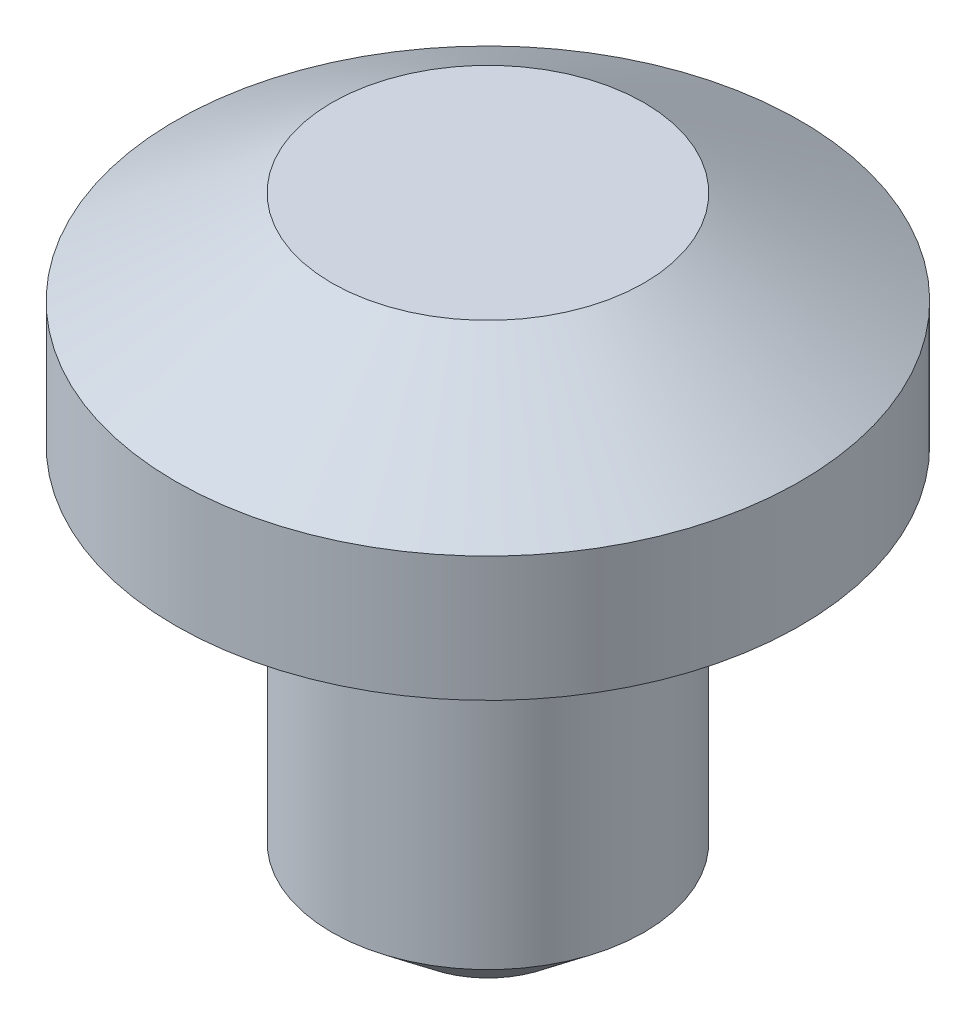
SolidWorks part; units mm, degrees
ref_plane "Front Plane" through (0, 0, 0) normal (0, 0, 1) x (1, 0, 0)
ref_plane "Top Plane" through (0, 0, 0) normal (0, 1, 0) x (1, 0, 0)
ref_plane "Right Plane" through (0, 0, 0) normal (1, 0, 0) x (0, 0, -1)
sketch "Sketch1" plane through (0, 0, 0) normal (0, 0, 1) x (1, 0, 0)
  line L0 (0, 63.5) -> (0, -63.5)
  line L1 (-31.75, -63.5) -> (0, -63.5)
  line L2 (-63.5, 0) -> (-63.5, 63.5)
  line L3 (-63.5, 63.5) -> (0, 63.5)
  line L4 (-63.5, 0) -> (-31.75, 0)
  line L5 (-31.75, 0) -> (-31.75, -63.5)
  line L6 (-63.5, 0) -> (0, 0) construction
  dimension "D2" = 63.5
  dimension "D4" = 31.75
  dimension "D3" = 63.5
revolve "Revolve1" add sketch "Sketch1" angle 360 about L0
sketch "Sketch3" plane through (0, 0, 0) normal (1, 0, 0) x (0, 0, -1)
  line L0 (-63.5, 0) -> (63.5, 0) construction
  line L1 (63.5, 63.5) -> (-63.5, 63.5) construction
  line L2 (-31.75, -63.5) -> (31.75, -63.5) construction
  line L3 (-63.5, 0) -> (63.5, 0)
  line L4 (0, 63.5) -> (-63.5, 63.5)
  line L5 (-31.75, -63.5) -> (0, -63.5)
  line L6 (-63.5, 63.5) -> (-63.5, 0)
  line L7 (-31.75, -63.5) -> (-31.75, 0)
  line L8 (-63.5, 19.05) -> (-90.7013, 19.05)
  line L9 (0, 63.5) -> (0, -63.5)
  line L10 (-63.5, 19.05) -> (-31.75, 0)
  line L11 (-90.7013, 44.45) -> (-63.5, 44.45)
  line L12 (-31.75, 0) -> (-31.75, 63.5)
  line L13 (-31.75, 63.5) -> (-63.5, 44.45)
  line L14 (-31.75, -50.8) -> (-53.2221, -50.8)
  line L15 (-31.75, -50.8) -> (-15.875, -63.5)
  dimension "D1" = 19.05
  dimension "D2" = 19.05
  dimension "D3" = 12.7
revolve "Cut-Revolve1" cut sketch "Sketch3" angle 360 about L9
